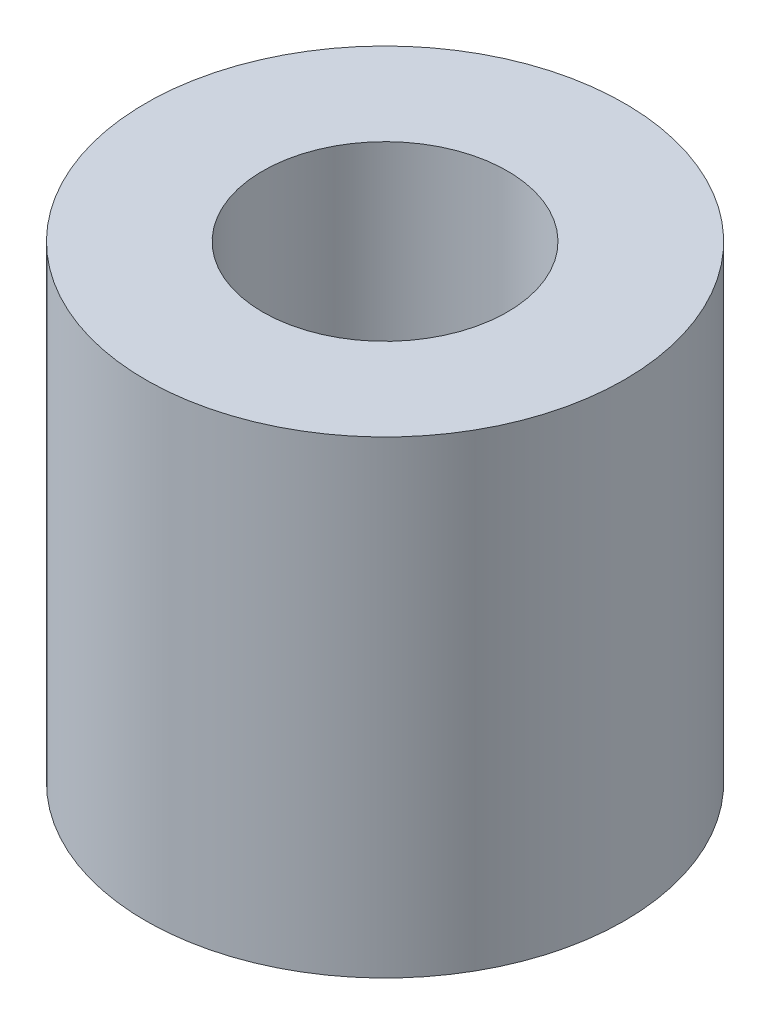
SolidWorks part; units mm, degrees
ref_plane "Front Plane" through (0, 0, 0) normal (0, 0, 1) x (1, 0, 0)
ref_plane "Top Plane" through (0, 0, 0) normal (0, 1, 0) x (1, 0, 0)
ref_plane "Right Plane" through (0, 0, 0) normal (1, 0, 0) x (0, 0, -1)
sketch "Sketch1" plane through (0, 0, 0) normal (0, 1, 0) x (1, 0, 0)
  circle A0 centre (0, 0) radius 2.61
  dimension "D1" = 5.22
extrude "Extrude-Thin1" add sketch "Sketch1" along normal blind 10 thin
